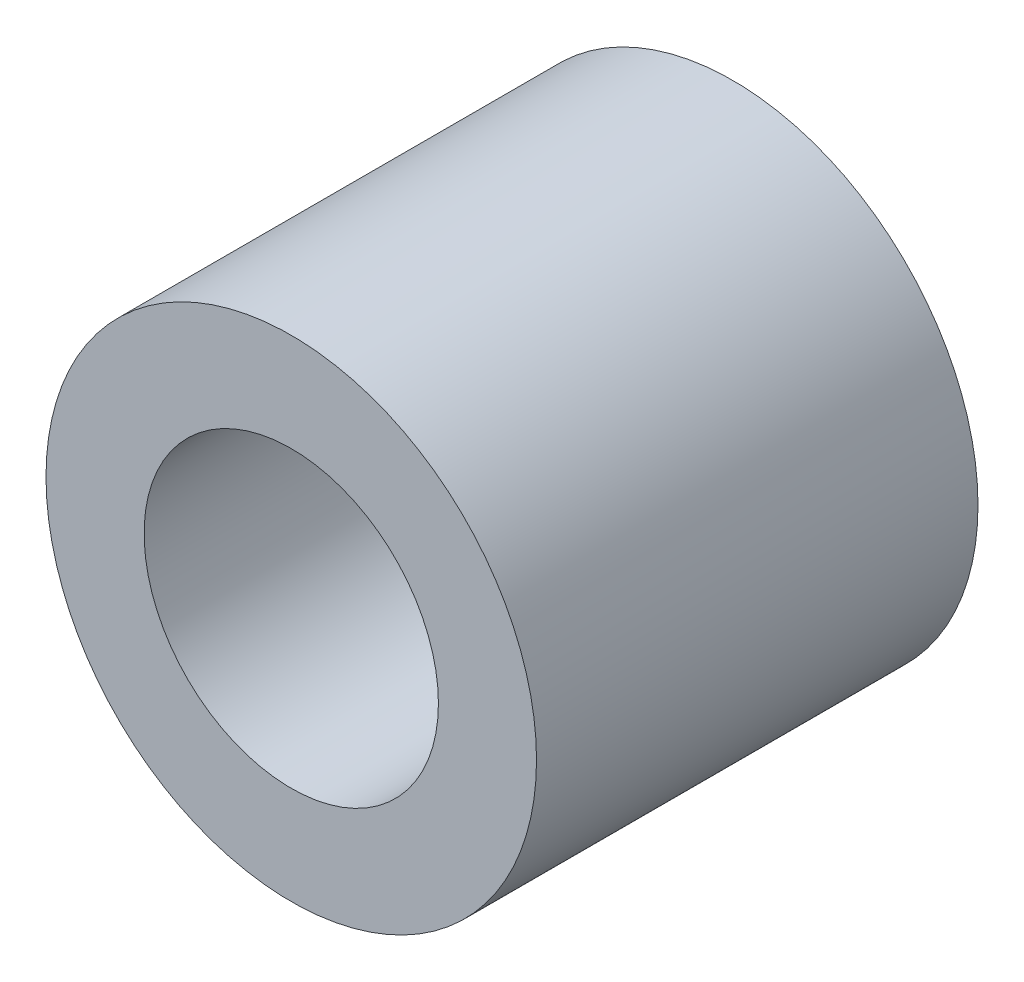
SolidWorks part; units mm, degrees
material "ﾎﾟﾘｵｷｼﾒﾁﾚﾝ(POM)ｱｾﾀｰﾙ共重合体"
ref_plane "Front Plane" through (0, 0, 0) normal (0, 0, 1) x (1, 0, 0)
ref_plane "Top Plane" through (0, 0, 0) normal (0, 1, 0) x (1, 0, 0)
ref_plane "Right Plane" through (0, 0, 0) normal (1, 0, 0) x (0, 0, -1)
sketch "Sketch2" plane through (0, 0, 0) normal (0, 0, 1) x (1, 0, 0)
  circle A0 centre (0, 0) radius 2.5
  circle A1 centre (0, 0) radius 1.5
  dimension "D1" = 3
  dimension "D2" = 5
  dimension "D3" = 5
extrude "Boss-Extrude1" add sketch "Sketch2" along normal blind 4.5
